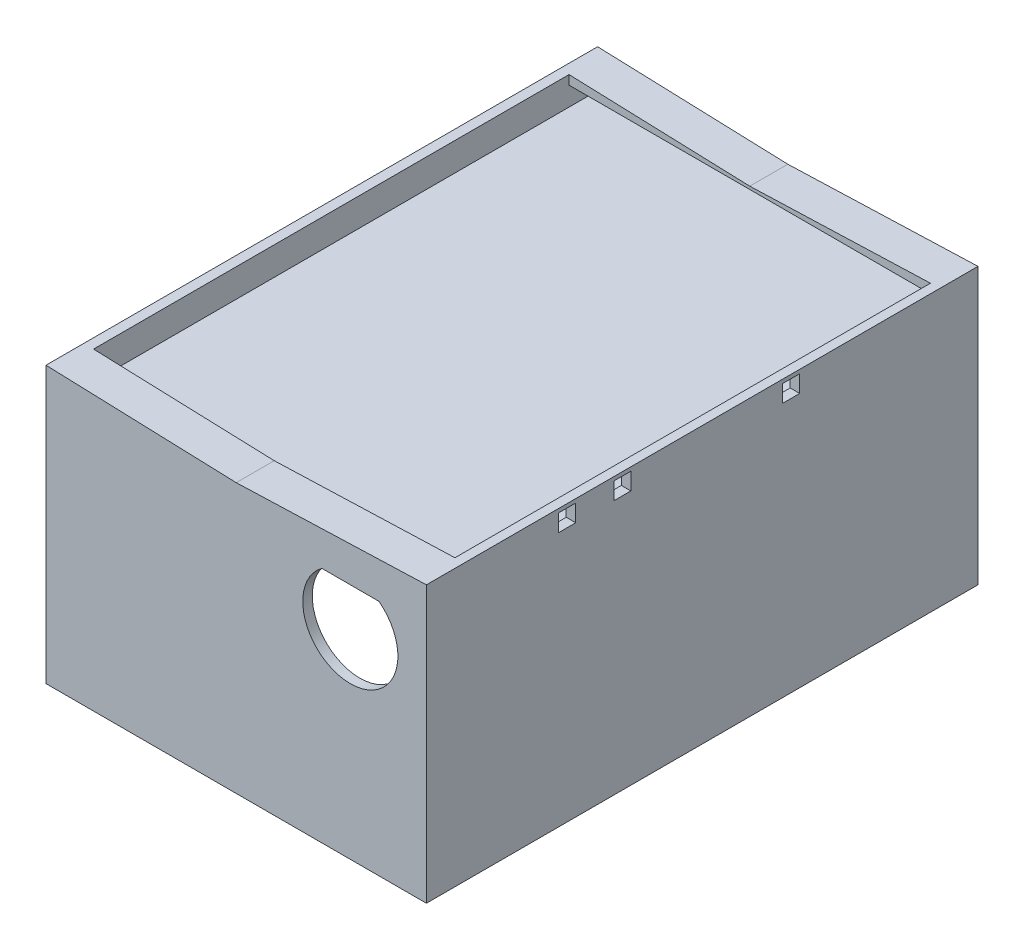
SolidWorks part; units mm, degrees
ref_plane "Front Plane" through (0, 0, 0) normal (0, 0, 1) x (1, 0, 0)
ref_plane "Top Plane" through (0, 0, 0) normal (0, 1, 0) x (1, 0, 0)
ref_plane "Right Plane" through (0, 0, 0) normal (1, 0, 0) x (0, 0, -1)
sketch "Sketch1" plane through (0, 0, 0) normal (0, 1, 0) x (1, 0, 0)
  line L1 (-96.0616, 57.1062) -> (103.9384, 57.1062)
  line L2 (-96.0616, 57.1062) -> (-96.0616, -232.8938)
  line L3 (-96.0616, -232.8938) -> (103.9384, -232.8938)
  line L4 (103.9384, 57.1062) -> (103.9384, -232.8938)
  dimension "D1" = 200
  dimension "D2" = 290
extrude "Boss-Extrude2" add sketch "Sketch1" along normal blind 10 contours L2 L3 L4 L1
sketch "Sketch2" plane through (0, 10, 0) normal (0, 1, 0) x (1, 0, 0)
  line L0 (-96.0616, -87.8938) -> (103.9384, -87.8938)
  line L1 (-96.0616, 57.1062) -> (-96.0616, -232.8938) construction
  line L2 (103.9384, 57.1062) -> (103.9384, -232.8938) construction
  line L3 (3.9384, 57.1062) -> (3.9384, -232.8938)
  line L4 (-96.0616, 57.1062) -> (103.9384, 57.1062) construction
  line L5 (-96.0616, -232.8938) -> (103.9384, -232.8938) construction
  line L7 (-91.0616, 52.1062) -> (98.9384, 52.1062)
  line L8 (-91.0616, 52.1062) -> (-91.0616, -227.8938)
  line L9 (-91.0616, -227.8938) -> (98.9384, -227.8938)
  line L10 (98.9384, 52.1062) -> (98.9384, -227.8938)
  line L11 (-91.0616, 52.1062) -> (98.9384, -227.8938) construction
  line L12 (-91.0616, -227.8938) -> (98.9384, 52.1062) construction
  point P12 (3.9384, -87.8938)
  line M3 (103.9384, 57.1062) -> (-96.0616, 57.1062)
  line M4 (-96.0616, 57.1062) -> (-96.0616, -232.8938)
  line M5 (-96.0616, -232.8938) -> (103.9384, -232.8938)
  line M6 (103.9384, -232.8938) -> (103.9384, 57.1062)
  dimension "D1" = 5
  dimension "D2" = 5
extrude "Boss-Extrude4" add sketch "Sketch2" along normal blind 140 contours L8 L7 L3 L0 M3 M4 | L7 L10 L0 L3 M6 M3 | L0 L10 L9 L3 M5 M6 | L9 L8 L0 L3 M4 M5
sketch "Sketch5" plane through (103.9384, 0, 0) normal (1, 0, 0) x (0, 0, -1)
  line L0 (-232.8938, 75) -> (-232.8938, 112.5)
  line L1 (-232.8938, 150) -> (-232.8938, 0) construction
  line L2 (-232.8938, 150) -> (57.1062, 150) construction
  line L5 (-129.8938, 143.5) -> (-41.1438, 143.5)
  line L7 (-163.3938, 148) -> (-154.3938, 148)
  line L8 (-163.3938, 148) -> (-163.3938, 139)
  line L9 (-163.3938, 139) -> (-154.3938, 139)
  line L10 (-154.3938, 148) -> (-154.3938, 139)
  line L11 (-163.3938, 148) -> (-154.3938, 139) construction
  line L12 (-163.3938, 139) -> (-154.3938, 148) construction
  line L13 (-134.3938, 148) -> (-125.3938, 148)
  line L14 (-134.3938, 148) -> (-134.3938, 139)
  line L15 (-134.3938, 139) -> (-125.3938, 139)
  line L16 (-125.3938, 148) -> (-125.3938, 139)
  line L17 (-134.3938, 148) -> (-125.3938, 139) construction
  line L18 (-134.3938, 139) -> (-125.3938, 148) construction
  line L19 (-45.6438, 148) -> (-36.6438, 148)
  line L20 (-45.6438, 148) -> (-45.6438, 139)
  line L21 (-45.6438, 139) -> (-36.6438, 139)
  line L22 (-36.6438, 148) -> (-36.6438, 139)
  line L23 (-45.6438, 148) -> (-36.6438, 139) construction
  line L24 (-45.6438, 139) -> (-36.6438, 148) construction
  point P9 (-158.8938, 143.5)
  dimension "D2" = 79.75
  dimension "D3" = 69.5
  dimension "D4" = 9
  dimension "D5" = 9
  dimension "D6" = 9
  dimension "D7" = 9
  dimension "D8" = 9
  dimension "D9" = 9
  dimension "D10" = 20
  dimension "D11" = 2
extrude "Cut-Extrude1" cut sketch "Sketch5" against normal blind 10 contours L19 L22 L21 L20 | L13 L16 L15 L14 | L7 L10 L9 L8
sketch "Sketch6" plane through (-96.0616, 0, 0) normal (-1, 0, 0) x (0, 0, 1)
  line L0 (87.8938, 150) -> (87.8938, 0)
  line L1 (-57.1062, 150) -> (232.8938, 150) construction
  line L2 (-57.1062, 0) -> (232.8938, 0) construction
  line L3 (232.8938, 150) -> (194.2563, 150)
  line L4 (-57.1062, 150) -> (-18.4687, 150)
  line L5 (194.2563, 150) -> (194.2563, 0)
  line L6 (-18.4687, 150) -> (-18.4687, 0)
  line L7 (-18.4687, 75) -> (-18.4687, 150)
  line L8 (194.2563, 150) -> (194.2563, 75)
  line L9 (194.2563, 150) -> (194.2563, 112.5)
  line L10 (-18.4687, 150) -> (-18.4687, 112.5)
  line L11 (194.2563, 112.5) -> (-18.4687, 112.5)
  line L12 (194.2563, 112.5) -> (189.2563, 112.5)
  line L13 (-18.4687, 112.5) -> (-13.4687, 112.5)
  line L14 (-13.4687, 112.5) -> (-13.4687, 61.57)
  line L15 (189.2563, 112.5) -> (189.2563, 61.57)
  circle A0 centre (189.2563, 112.5) radius 3.78
  circle A1 centre (-13.4687, 112.5) radius 3.78
  circle A2 centre (189.2563, 61.57) radius 3.78
  circle A3 centre (-13.4687, 61.57) radius 3.78
  dimension "D7" = 7.56
  dimension "D8" = 7.56
  dimension "D11" = 7.56
  dimension "D12" = 7.56
  dimension "D1" = 38.6375
  dimension "D2" = 38.6375
  dimension "D3" = 37.5
  dimension "D4" = 37.5
  dimension "D5" = 5
  dimension "D6" = 5
  dimension "D9" = 50.93
  dimension "D10" = 50.93
extrude "Cut-Extrude2" cut sketch "Sketch6" against normal blind 10 contours A0 | A2 | A3 | A1
sketch "Sketch7" plane through (0, 0, 232.8938) normal (0, 0, 1) x (1, 0, 0)
  line L0 (103.9384, 150) -> (103.9384, 0) construction
  line L1 (-96.0616, 150) -> (103.9384, 150) construction
  circle A0 centre (63.9384, 110) radius 25
  dimension "D1" = 50
  dimension "D2" = 40
  dimension "D3" = 40
extrude "Cut-Extrude3" cut sketch "Sketch7" against normal blind 10 contours A0
sketch "Sketch8" plane through (0, 10, 0) normal (0, 1, 0) x (1, 0, 0)
  line L1 (-91.0616, 52.1062) -> (98.9384, 52.1062)
  line L2 (-91.0616, 52.1062) -> (-91.0616, -227.8938)
  line L3 (-91.0616, -227.8938) -> (98.9384, -227.8938)
  line L4 (98.9384, 52.1062) -> (98.9384, -227.8938)
extrude "Cut-Extrude4" cut sketch "Sketch8" against normal blind 10
sketch "Sketch9" plane through (0, 0, 0) normal (0, -1, 0) x (1, 0, 0)
  line L1 (-102.3219, 239.6938) -> (109.1358, 239.6938)
  line L2 (-102.3219, 239.6938) -> (-102.3219, -61.6829)
  line L3 (-102.3219, -61.6829) -> (109.1358, -61.6829)
  line L4 (109.1358, 239.6938) -> (109.1358, -61.6829)
extrude "Cut-Extrude5" cut sketch "Sketch9" against normal blind 5
sketch "Sketch10" plane through (0, 0, 227.8938) normal (0, 0, -1) x (-1, 0, 0)
  line L0 (96.0616, 150) -> (96.0616, 5) construction
  line L1 (-103.9384, 150) -> (96.0616, 150)
  line L2 (-103.9384, 150) -> (-103.9384, 145)
  line L3 (-103.9384, 145) -> (96.0616, 145)
  line L4 (96.0616, 150) -> (96.0616, 145)
  dimension "D1" = 5
extrude "Boss-Extrude7" add sketch "Sketch10" along normal blind 15 contours L1 L4 L3 L2
sketch "Sketch12" plane through (0, 0, -52.1062) normal (0, 0, 1) x (1, 0, 0)
  line L0 (103.9384, 150) -> (103.9384, 5) construction
  line L1 (-96.0616, 150) -> (103.9384, 150)
  line L2 (-96.0616, 150) -> (-96.0616, 145)
  line L3 (-96.0616, 145) -> (103.9384, 145)
  line L4 (103.9384, 150) -> (103.9384, 145)
  dimension "D1" = 5
extrude "Boss-Extrude8" add sketch "Sketch12" along normal blind 15
sketch "Sketch13" plane through (-91.0616, 0, 0) normal (1, 0, 0) x (0, 0, -1)
  line L0 (-232.8938, 150) -> (-232.8938, 5) construction
  line L1 (-232.8938, 135) -> (57.1062, 135)
  line L2 (-232.8938, 135) -> (-232.8938, 130)
  line L3 (-232.8938, 130) -> (57.1062, 130)
  line L4 (57.1062, 135) -> (57.1062, 130)
  line L5 (57.1062, 150) -> (57.1062, 5) construction
  line L6 (-232.8938, 150) -> (57.1062, 150) construction
  dimension "D1" = 5
  dimension "D2" = 15
extrude "Boss-Extrude14" add sketch "Sketch13" along normal blind 190 contours L1 L4 L3 L2
sketch "Sketch17" plane through (0, 0, 232.8938) normal (0, 0, 1) x (1, 0, 0)
  line L0 (-96.0616, 150) -> (3.9384, 150)
  line L1 (-96.0616, 150) -> (103.9384, 150) construction
  line L2 (3.9384, 150) -> (3.9384, 146.51)
  line L3 (3.9384, 146.51) -> (-96.0616, 150)
  line L4 (3.9384, 146.51) -> (103.9384, 150)
  line L5 (103.9384, 150) -> (-96.0616, 150)
  line M7 (103.9384, 150) -> (-96.0616, 150)
  dimension "D1" = 100
  dimension "D2" = 3.49
extrude "Cut-Extrude6" cut sketch "Sketch17" against normal blind 300 contours L3 L2 M7 | L2 L4 M7
sketch "Sketch18" plane through (0, 135, 0) normal (0, 1, 0) x (1, 0, 0)
  line L0 (3.9384, -232.8938) -> (103.9384, -232.8938) construction
  line L1 (85.1339, -45.6438) -> (94.1339, -45.6438)
  line L2 (85.1339, -45.6438) -> (85.1339, -36.6438)
  line L3 (85.1339, -36.6438) -> (94.1339, -36.6438)
  line L4 (94.1339, -45.6438) -> (94.1339, -36.6438)
  line L5 (85.1339, -45.6438) -> (94.1339, -36.6438) construction
  line L6 (85.1339, -36.6438) -> (94.1339, -45.6438) construction
  line L7 (86.673, -134.3938) -> (95.673, -134.3938)
  line L8 (86.673, -134.3938) -> (86.673, -125.3938)
  line L9 (86.673, -125.3938) -> (95.673, -125.3938)
  line L10 (95.673, -134.3938) -> (95.673, -125.3938)
  line L11 (86.673, -134.3938) -> (95.673, -125.3938) construction
  line L12 (86.673, -125.3938) -> (95.673, -134.3938) construction
  line L13 (86.673, -163.3938) -> (95.673, -163.3938)
  line L14 (86.673, -163.3938) -> (86.673, -154.3938)
  line L15 (86.673, -154.3938) -> (95.673, -154.3938)
  line L16 (95.673, -163.3938) -> (95.673, -154.3938)
  line L17 (86.673, -163.3938) -> (95.673, -154.3938) construction
  line L18 (86.673, -154.3938) -> (95.673, -163.3938) construction
  point P0 (89.6339, -41.1438)
  point P5 (91.173, -129.8938)
  point P10 (91.173, -158.8938)
  dimension "D1" = 9
  dimension "D2" = 9
  dimension "D3" = 9
  dimension "D4" = 9
  dimension "D5" = 9
  dimension "D6" = 9
  dimension "D7" = 20
  dimension "D8" = 79.75
  dimension "D9" = 69.5
extrude "Cut-Extrude7" cut sketch "Sketch18" against normal blind 10
